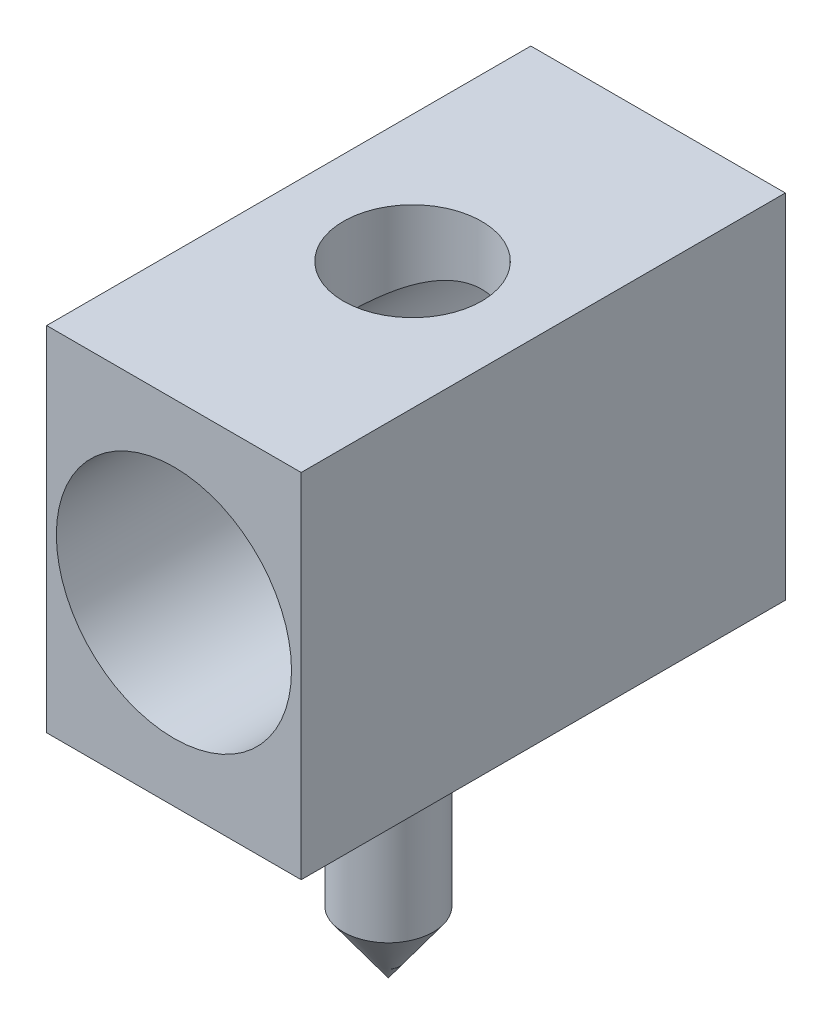
SolidWorks part; units mm, degrees
material "Chrome Stainless Steel"
ref_plane "Front Plane" through (0, 0, 0) normal (0, 0, 1) x (1, 0, 0)
ref_plane "Top Plane" through (0, 0, 0) normal (0, 1, 0) x (1, 0, 0)
ref_plane "Right Plane" through (0, 0, 0) normal (1, 0, 0) x (0, 0, -1)
sketch "Sketch1" plane through (0, 0, 0) normal (0, 1, 0) x (1, 0, 0)
  line L1 (0, 0) -> (-3.68, 0)
  line L2 (0, 0) -> (0, -7)
  line L3 (0, -7) -> (-3.68, -7)
  line L4 (-3.68, 0) -> (-3.68, -7)
  dimension "D1" = 7
  dimension "D2" = 3.68
extrude "Boss-Extrude1" add sketch "Sketch1" along normal blind 5.1
sketch "Sketch2" plane through (0, 0, 7) normal (0, 0, 1) x (1, 0, 0)
  line L0 (-3.68, 0) -> (0, 0) construction
  line L1 (-3.68, 5.1) -> (-3.68, 0) construction
  circle A0 centre (-1.84, 2.55) radius 1.7
  point P5 (-1.84, 0)
  point P9 (-3.68, 2.55)
  dimension "D1" = 3.4
extrude "Cut-Extrude1" cut sketch "Sketch2" against normal offset from surface (6.5 mm away) 0.5 up to face at (-1.84, 2.55, 0)
sketch "Sketch3" plane through (0, 0, 0) normal (0, -1, 0) x (1, 0, 0)
  line L0 (-3.68, 7) -> (0, 7) construction
  line L2 (-3.68, 0) -> (-3.68, 7) construction
  circle A0 centre (-1.84, 3.9) radius 0.65
  dimension "D1" = 1.3
  dimension "D2" = 3.1
  dimension "D3" = 1.84
extrude "Boss-Extrude2" add sketch "Sketch3" along normal blind 2.8
sketch "Sketch4" plane through (0, 5.1, 0) normal (0, 1, 0) x (1, 0, 0)
  line L1 (-3.68, 0) -> (-3.68, -7) construction
  line L3 (0, 0) -> (-3.68, 0) construction
  circle A0 centre (-1.84, -3.55) radius 1
  dimension "D1" = 2
  dimension "D2" = 1.84
  dimension "D3" = 3.55
extrude "Cut-Extrude2" cut sketch "Sketch4" against normal up to next
ref_plane "Plane1" through (-1.84, 0, 0) normal (1, 0, 0) x (0, 0, -1)
sketch "Sketch7" plane through (-1.84, 0, 0) normal (1, 0, 0) x (0, 0, -1)
  line L0 (-3.9, -2.8) -> (-3.9, -3.7)
  line L1 (-4.55, -2.8) -> (-3.25, -2.8) construction
  line L2 (-3.9, -3.7) -> (-4.55, -2.8)
  line L3 (-4.55, -2.8) -> (-3.9, -2.8)
  dimension "D1" = 0.9
revolve "Revolve2" add sketch "Sketch7" angle 360 about L0
